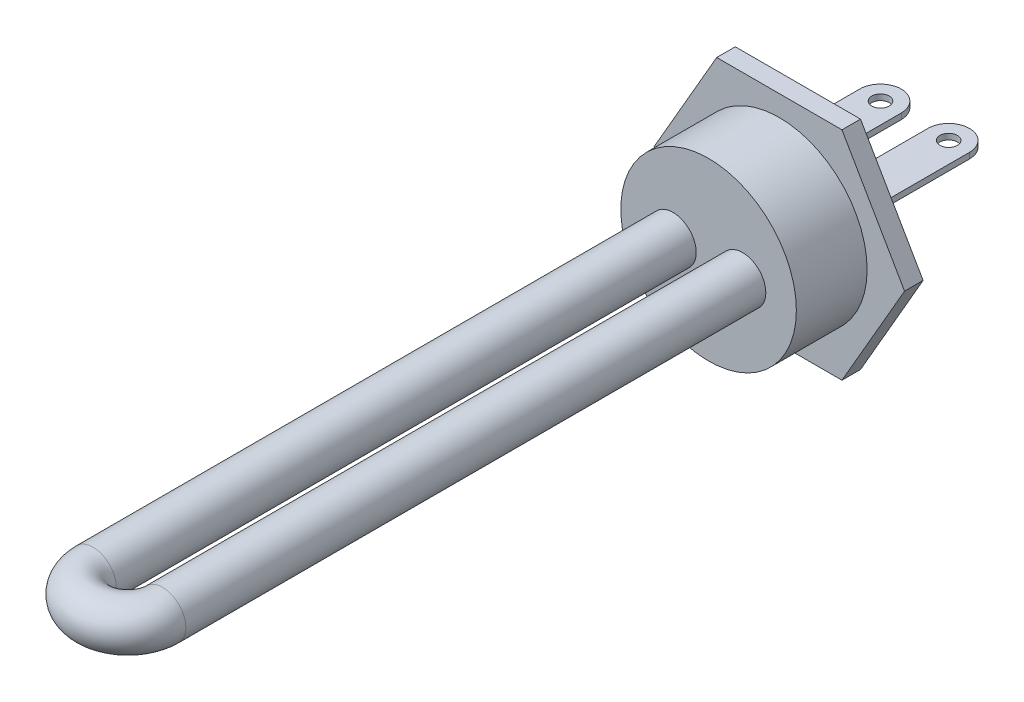
SolidWorks part; units mm, degrees
ref_plane "Front Plane" through (0, 0, 0) normal (0, 0, 1) x (1, 0, 0)
ref_plane "Top Plane" through (0, 0, 0) normal (0, 1, 0) x (1, 0, 0)
ref_plane "Right Plane" through (0, 0, 0) normal (1, 0, 0) x (0, 0, -1)
sketch "Sketch1" plane through (0, 0, 0) normal (0, 0, 1) x (1, 0, 0)
  line L0 (55, 0) -> (-55, 0) construction
  line L1 (10.7965, -18.7) -> (21.5929, 0)
  line L2 (21.5929, 0) -> (10.7965, 18.7)
  line L3 (10.7965, 18.7) -> (-10.7965, 18.7)
  line L4 (-10.7965, 18.7) -> (-21.5929, 0)
  line L5 (-21.5929, 0) -> (-10.7965, -18.7)
  line L6 (-10.7965, -18.7) -> (10.7965, -18.7)
  circle A0 centre (0, 0) radius 18.7 construction
  dimension "D1" = 37.4
extrude "Boss-Extrude1" add sketch "Sketch1" along normal blind 3.2
sketch "Sketch2" plane through (0, 0, 3.2) normal (0, 0, 1) x (1, 0, 0)
  circle A0 centre (0, 0) radius 15.135
  dimension "D1" = 30.27
extrude "Boss-Extrude2" add sketch "Sketch2" along normal blind 12.2
sketch "Sketch3" plane through (0, 0, 0) normal (0, 0, -1) x (-1, 0, 0)
  circle A0 centre (0, 0) radius 13.5
  dimension "D1" = 27
extrude "Cut-Extrude1" cut sketch "Sketch3" against normal blind 12.8
sketch "Sketch4" plane through (0, 0, 0) normal (0, 1, 0) x (1, 0, 0)
  line L0 (-6.135, 0) -> (-6.135, -115.4)
  line L1 (5.865, 0) -> (5.865, -115.4)
  line L3 (10.7965, 0) -> (-10.7965, 0) construction
  line L4 (-15.135, -15.4) -> (15.135, -15.4) construction
  line L5 (-15.135, -3.2) -> (-15.135, -15.4) construction
  arc A0 (-6.135, -115.4) -> (5.865, -115.4) centre (-0.135, -115.4) ccw
  dimension "D1" = 12
  dimension "D2" = 100
  dimension "D3" = 9
sweep "Sweep1" add path "Sketch4" circular profile diameter 8 parameters "D3"=8
sketch "Sketch29" plane through (0, 0, 0) normal (0, 0, -1) x (-1, 0, 0)
  circle A0 centre (-5.865, 0) radius 4.1
  circle A1 centre (6.135, 0) radius 4.1
  dimension "D1" = 8.2
  dimension "D2" = 8.2
extrude "Boss-Extrude4" add sketch "Sketch29" along normal blind 5.7
sketch "Sketch33" plane through (0, 0, -5.7) normal (0, 0, -1) x (-1, 0, 0)
  line L1 (-9.46, 3) -> (-2.3, 3)
  line L2 (-9.46, 3) -> (-9.46, 2)
  line L3 (-9.46, 2) -> (-2.3, 2)
  line L4 (-2.3, 3) -> (-2.3, 2)
  line L5 (2.3, 3) -> (9.46, 3)
  line L6 (2.3, 3) -> (2.3, 2)
  line L7 (2.3, 2) -> (9.46, 2)
  line L8 (9.46, 3) -> (9.46, 2)
  circle A1 centre (-5.865, 0) radius 4.1 construction
  dimension "D7" = 2
  dimension "D1" = 7.16
  dimension "D2" = 7.16
  dimension "D3" = 1
  dimension "D4" = 1
  dimension "D5" = 2.3
  dimension "D6" = 2.3
extrude "Boss-Extrude5" add sketch "Sketch33" along normal blind 18
sketch "Sketch34" plane through (0, 3, 0) normal (0, 1, 0) x (1, 0, 0)
  line L1 (9.46, 20.12) -> (9.46, 23.7)
  line L2 (9.46, 23.7) -> (2.3, 23.7)
  line L3 (2.3, 23.7) -> (2.3, 20.12)
  line L4 (-2.3, 20.12) -> (-2.3, 23.7)
  line L5 (-2.3, 23.7) -> (-9.46, 23.7)
  line L6 (-9.46, 23.7) -> (-9.46, 20.12)
  arc A0 (-2.3, 20.12) -> (-9.46, 20.12) centre (-5.88, 20.12) ccw
  arc A1 (9.46, 20.12) -> (2.3, 20.12) centre (5.88, 20.12) ccw
  circle A2 centre (-5.88, 20.12) radius 1.5
  circle A3 centre (5.88, 20.12) radius 1.5
  line M6 (9.46, 5.7) -> (9.46, 23.7)
  line M7 (9.46, 23.7) -> (2.3, 23.7)
  line M8 (2.3, 23.7) -> (2.3, 5.7)
  dimension "D1" = 3
  dimension "D2" = 3
extrude "Cut-Extrude2" cut sketch "Sketch34" against normal through all contours A0 L5 L6 | A0 L4 L5 | A1 L2 M8 | A1 M6 M7 | A2 | A3
